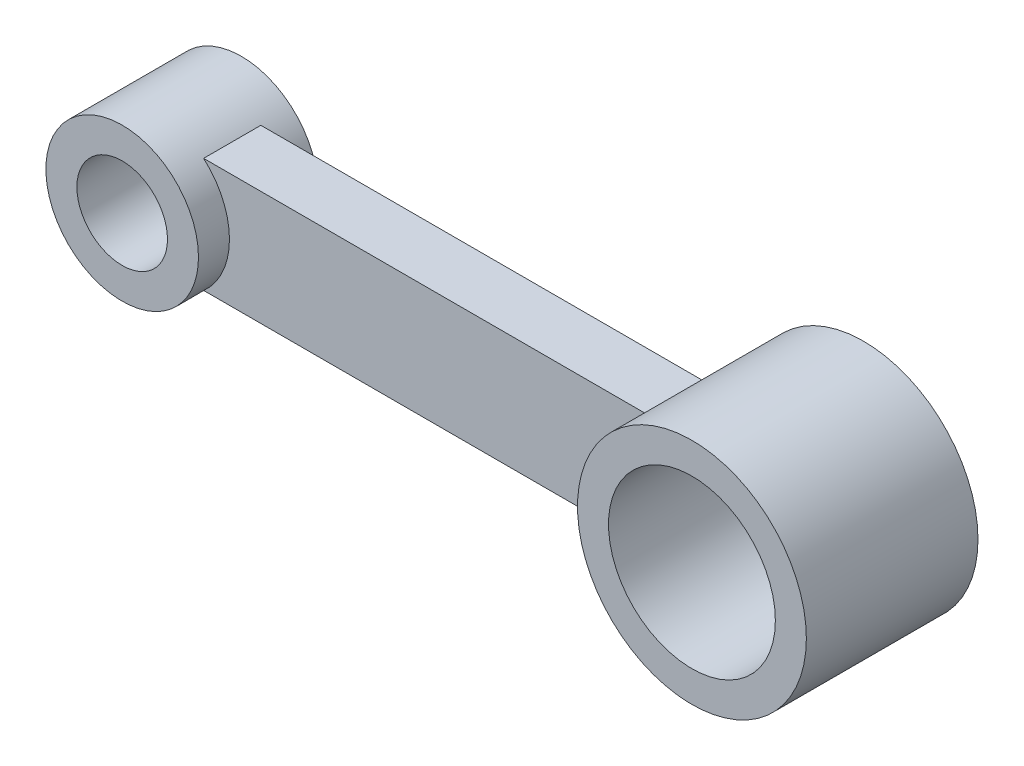
SolidWorks part; units mm, degrees
ref_plane "Front Plane" through (0, 0, 0) normal (0, 0, 1) x (1, 0, 0)
ref_plane "Top Plane" through (0, 0, 0) normal (0, 1, 0) x (1, 0, 0)
ref_plane "Right Plane" through (0, 0, 0) normal (1, 0, 0) x (0, 0, -1)
sketch "Sketch2" plane through (0, 0, 0) normal (0, 0, 1) x (1, 0, 0)
  line L0 (10.2092, -12.3196) -> (10.5262, -12.0498)
  line L1 (104.2154, -12) -> (10.2092, -12)
  line L2 (104.2154, 12) -> (10.583, 12)
  circle A0 centre (0, 0) radius 16
  circle A1 centre (0, 0) radius 9.5
  circle A2 centre (125, 0) radius 24
  circle A3 centre (125, 0) radius 17.5
  dimension "D1" = 19
  dimension "D2" = 32
  dimension "D3" = 48
  dimension "D4" = 35
  dimension "D5" = 125
  dimension "D6" = 12
  dimension "D7" = 24
extrude "Boss-Extrude1" add sketch "Sketch2" along normal blind 36
sketch "Sketch3" plane through (0, 0, 0) normal (0, 0, -1) x (-1, 0, 0)
  line L0 (-104.2154, 12) -> (-10.583, 12)
  line L1 (-104.2154, -12) -> (-10.583, -12)
  arc A0 (-104.2154, -12) -> (-104.2154, 12) centre (-126.0804, 0) ccw
  arc A1 (-10.583, -12) -> (-10.583, 12) centre (1.417, 0) cw
extrude "Cut-Extrude1" cut sketch "Sketch3" against normal blind 12
sketch "Sketch4" plane through (0, 0, 36) normal (0, 0, 1) x (1, 0, 0)
  line L0 (10.583, 12) -> (104.2154, 12)
  line L1 (10.3677, -12.1847) -> (104.2154, -12)
  line L2 (10.2092, -12.3196) -> (10.5262, -12.0498) construction
  arc A0 (10.583, 12) -> (10.3677, -12.1847) centre (-1.617, 0.0153) cw
  arc A1 (104.2154, 12) -> (104.2154, -12) centre (125, 0) ccw
  dimension "D1" = 24
extrude "Cut-Extrude2" cut sketch "Sketch4" against normal blind 12
sketch "Sketch6" plane through (0, 0, 36) normal (0, 0, 1) x (1, 0, 0)
  circle A0 centre (0, 0) radius 9.5
  circle A1 centre (0, 0) radius 16
  dimension "D1" = 19
  dimension "D2" = 32
extrude "Cut-Extrude3" cut sketch "Sketch6" against normal blind 5.5
sketch "Sketch7" plane through (0, 0, 0) normal (0, 0, -1) x (-1, 0, 0)
  circle A0 centre (0, 0) radius 9.5
  circle A1 centre (0, 0) radius 16
extrude "Cut-Extrude4" cut sketch "Sketch7" against normal blind 5.5
sketch "Sketch8" plane through (0, 0, 0) normal (0, 0, -1) x (-1, 0, 0)
  circle A0 centre (-125, 0) radius 24
  circle A1 centre (-125, 0) radius 17.5
extrude "Boss-Extrude2" add sketch "Sketch8" against normal blind 36
sketch "Sketch9" plane through (0, 0, 5.5) normal (0, 0, -1) x (-1, 0, 0)
  circle A0 centre (0, 0) radius 16
  circle A1 centre (0, 0) radius 9.5
  dimension "D1" = 19
extrude "Boss-Extrude4" add sketch "Sketch9" against normal blind 25
